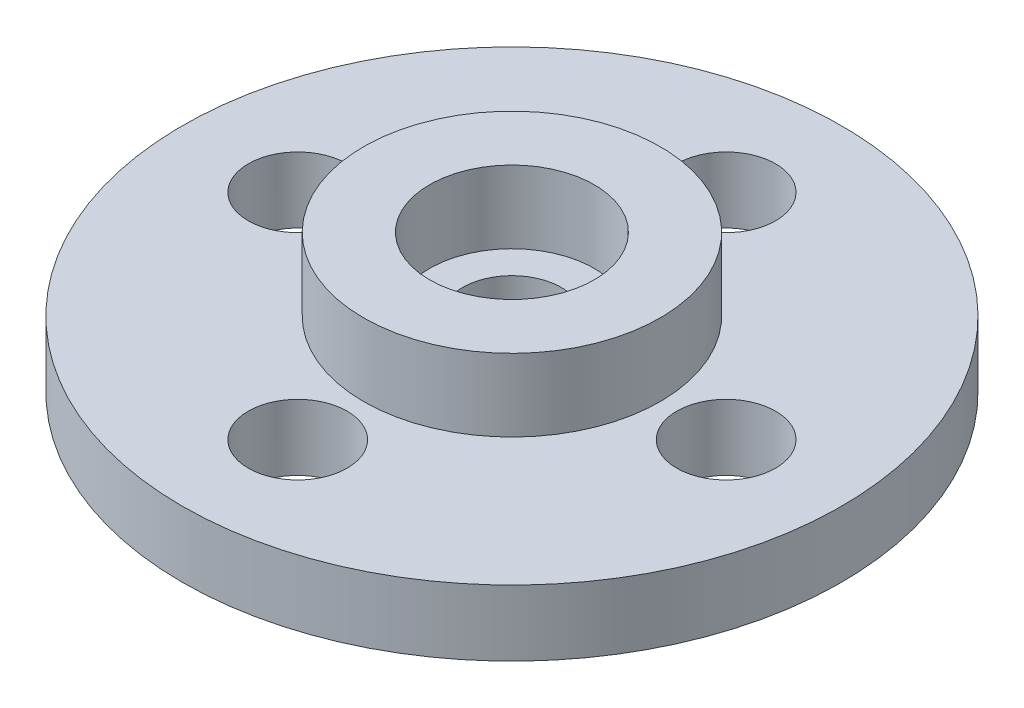
SolidWorks part; units mm, degrees
ref_plane "前视基准面" through (0, 0, 0) normal (0, 0, 1) x (1, 0, 0)
ref_plane "上视基准面" through (0, 0, 0) normal (0, 1, 0) x (1, 0, 0)
ref_plane "右视基准面" through (0, 0, 0) normal (1, 0, 0) x (0, 0, -1)
sketch "草图1" plane through (0, 0, 0) normal (0, 1, 0) x (1, 0, 0)
  circle A0 centre (0, 0) radius 10
  circle A2 centre (0, 6.5) radius 1.5
  circle A3 centre (0, -6.5) radius 1.5
  circle A4 centre (6.5, 0) radius 1.5
  circle A5 centre (-6.5, 0) radius 1.5
  circle A6 centre (0, 0) radius 1.5
extrude "凸台-拉伸1" add sketch "草图1" along normal blind 4.2
sketch "草图2" plane through (0, 4.2, 0) normal (0, 1, 0) x (1, 0, 0)
  circle A0 centre (0, 0) radius 2.5
  circle A1 centre (0, 0) radius 4.5
  circle A2 centre (0, 0) radius 10
  circle A3 centre (0, 6.5) radius 1.5
  circle A4 centre (-6.5, 0) radius 1.5
  circle A5 centre (6.5, 0) radius 1.5
  circle A6 centre (0, -6.5) radius 1.5
  circle A7 centre (0, 0) radius 1.5 construction
  circle M1 centre (6.5, 0) radius 1.5
  circle M2 centre (0, 6.5) radius 1.5
  circle M3 centre (0, 0) radius 10
  circle M4 centre (0, 0) radius 1.5
  circle M5 centre (0, -6.5) radius 1.5
  circle M6 centre (-6.5, 0) radius 1.5
extrude "切除-拉伸1" cut sketch "草图2" against normal blind 2.2 contours A1 M3 M2 M6 M5 M1 | A0 M4
